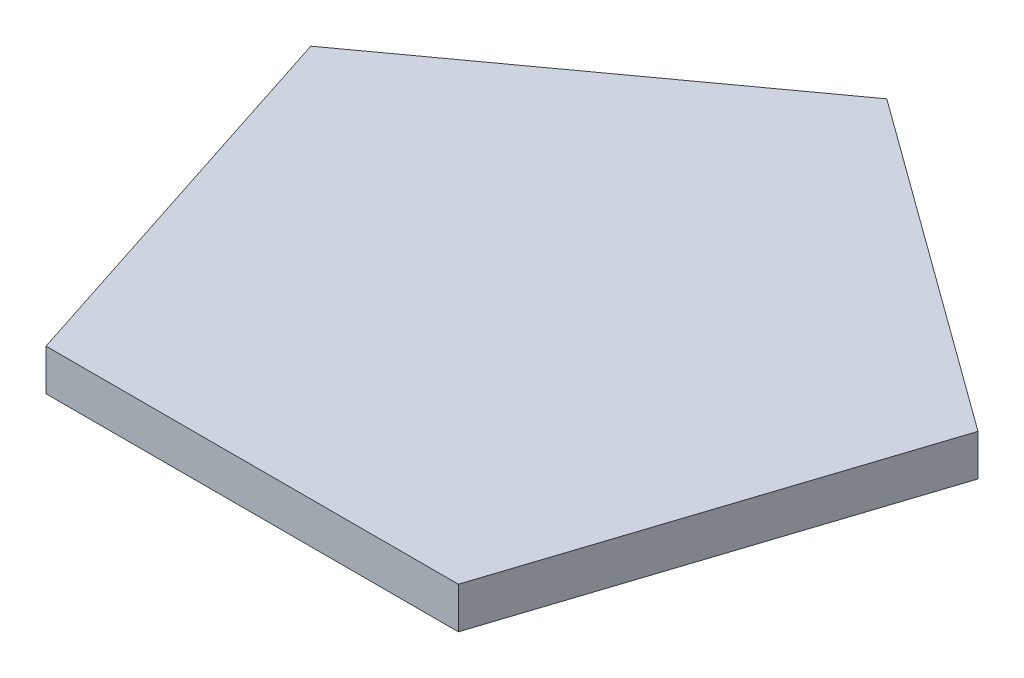
SolidWorks part; units mm, degrees
ref_plane "Front Plane" through (0, 0, 0) normal (0, 0, 1) x (1, 0, 0)
ref_plane "Top Plane" through (0, 0, 0) normal (0, 1, 0) x (1, 0, 0)
ref_plane "Right Plane" through (0, 0, 0) normal (1, 0, 0) x (0, 0, -1)
sketch "Sketch1" plane through (0, 0, 0) normal (0, 1, 0) x (1, 0, 0)
  line L1 (0, 21.6065) -> (-20.549, 6.6768)
  line L2 (-20.549, 6.6768) -> (-12.7, -17.4801)
  line L3 (-12.7, -17.4801) -> (12.7, -17.4801)
  line L4 (12.7, -17.4801) -> (20.549, 6.6768)
  line L5 (20.549, 6.6768) -> (0, 21.6065)
  circle A0 centre (0, 0) radius 17.4801 construction
  dimension "D1" = 25.4
extrude "Boss-Extrude1" add sketch "Sketch1" along normal blind 2.54
equation "\"edge\" = 1"
equation "\"D1@Sketch1\"=\"edge\""
